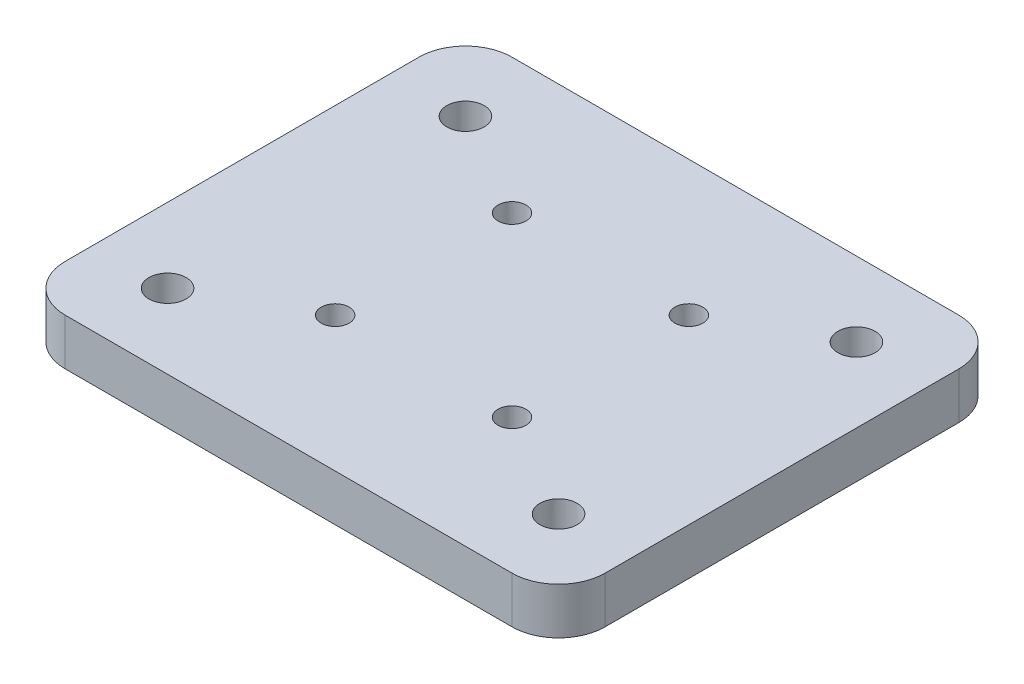
SolidWorks part; units mm, degrees
material "ABS"
ref_plane "Front Plane" through (0, 0, 0) normal (0, 0, 1) x (1, 0, 0)
ref_plane "Top Plane" through (0, 0, 0) normal (0, 1, 0) x (1, 0, 0)
ref_plane "Right Plane" through (0, 0, 0) normal (1, 0, 0) x (0, 0, -1)
sketch "Sketch1" plane through (0, 0, 0) normal (0, 1, 0) x (1, 0, 0)
  line L1 (-29, -24) -> (29, -24)
  line L2 (-29, -24) -> (-29, 24)
  line L3 (-29, 24) -> (29, 24)
  line L4 (29, -24) -> (29, 24)
  line L5 (-29, -24) -> (29, 24) construction
  line L6 (-29, 24) -> (29, -24) construction
  point P0 (0, 0)
  dimension "D1" = 58
  dimension "D2" = 48
extrude "Boss-Extrude1" add sketch "Sketch1" along normal blind 5
ref_point "Point1"
sketch "Sketch2" plane through (0, 5, 0) normal (0, 1, 0) x (1, 0, 0)
  line L0 (29, -24) -> (29, -16) construction
  line L1 (29, -24) -> (29, 24) construction
  line L2 (29, -16) -> (21, -16) construction
  line L3 (0, -2.75) -> (0, 2.75) construction
  line L4 (-9.5, 9.5) -> (9.5, 9.5) construction
  line L5 (-2.75, 0) -> (2.75, 0) construction
  line L6 (21, 16) -> (-21, 16) construction
  line L7 (-21, -9.5) -> (-9.5, -9.5) construction
  line L8 (-21, -16) -> (21, -16) construction
  line L9 (21, -16) -> (21, 16) construction
  line L10 (-21, -16) -> (-21, -9.5) construction
  line L11 (-9.5, -9.5) -> (-9.5, 9.5) construction
  line L12 (9.5, 9.5) -> (9.5, -9.5) construction
  line L13 (9.5, -9.5) -> (-9.5, -9.5) construction
  circle A0 centre (21, -16) radius 2
  circle A1 centre (-21, -16) radius 2
  circle A2 centre (-21, 16) radius 2
  circle A3 centre (21, 16) radius 2
  circle A4 centre (9.5, -9.5) radius 1.5
  circle A5 centre (-9.5, -9.5) radius 1.5
  circle A6 centre (9.5, 9.5) radius 1.5
  circle A7 centre (-9.5, 9.5) radius 1.5
  dimension "D3" = 4
  dimension "D6" = 3
  dimension "D1" = 8
  dimension "D2" = 8
  dimension "D4" = 6.5
  dimension "D5" = 11.5
extrude "Cut-Extrude1" cut sketch "Sketch2" against normal up to surface (5 mm away) up to face at (0, 0, 0)
fillet "Fillet1" radius 5 1 edges at (-29, 2.5, 24)
fillet "Fillet2" radius 5 1 edges at (29, 2.5, 24)
fillet "Fillet3" radius 5 1 edges at (29, 2.5, -24)
fillet "Fillet4" radius 5 1 edges at (-29, 2.5, -24)
